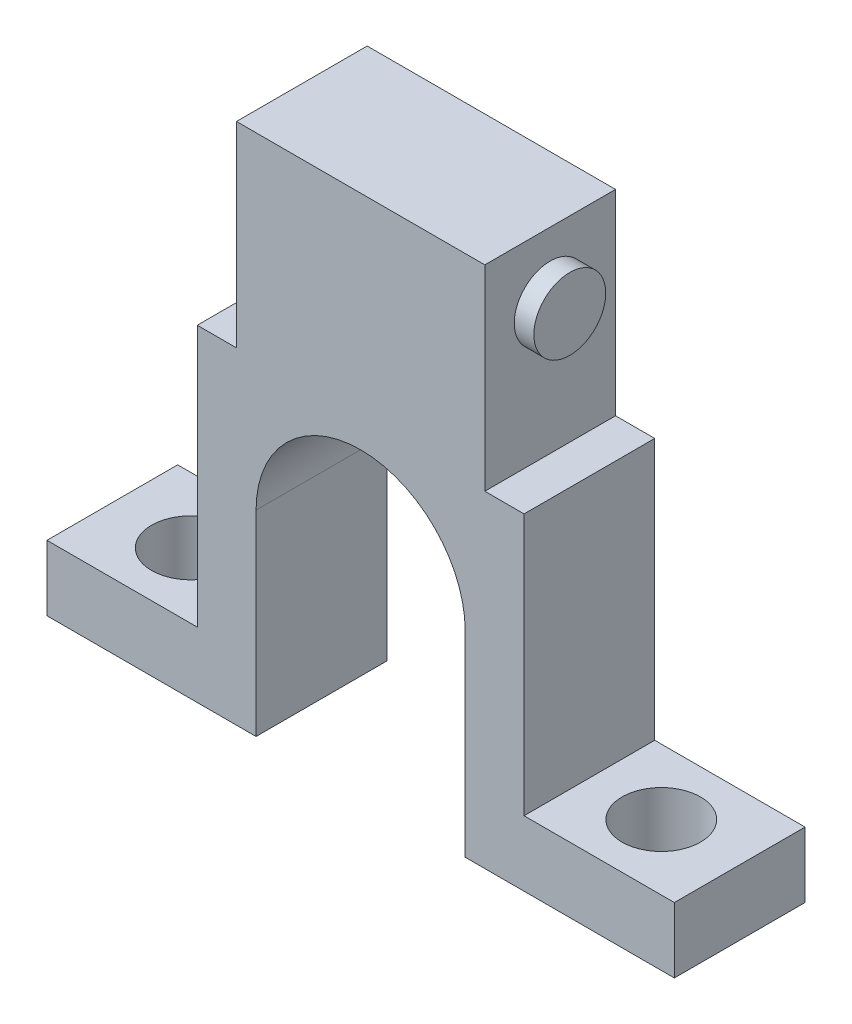
SolidWorks part; units mm, degrees
ref_plane "Front Plane" through (0, 0, 0) normal (0, 0, 1) x (1, 0, 0)
ref_plane "Top Plane" through (0, 0, 0) normal (0, 1, 0) x (1, 0, 0)
ref_plane "Right Plane" through (0, 0, 0) normal (1, 0, 0) x (0, 0, -1)
sketch "Sketch1" plane through (0, 0, 0) normal (0, 0, 1) x (1, 0, 0)
  line L0 (0, 0) -> (0, 17.5) construction
  line L1 (-9.5, 17.5) -> (9.5, 17.5)
  line L2 (9.5, 2.5) -> (12.5, 2.5)
  line L3 (-12.5, -17.5) -> (12.5, -17.5)
  line L4 (12.5, 2.5) -> (12.5, -17.5)
  line L5 (0, 0) -> (0, -17.5) construction
  line L6 (9.5, 17.5) -> (9.5, 2.5)
  line L7 (-9.5, 2.5) -> (-12.5, 2.5)
  line L8 (-9.5, 17.5) -> (-9.5, 2.5)
  line L9 (-12.5, 2.5) -> (-12.5, -17.5)
  dimension "D1" = 19
  dimension "D2" = 35
  dimension "D3" = 25
  dimension "D4" = 15
extrude "Boss-Extrude1" add sketch "Sketch1" along normal mid plane 10
sketch "Sketch4" plane through (0, 0, 0) normal (1, 0, 0) x (0, 0, -1)
  line L0 (0, 12.5) -> (0, 0) construction
  line L2 (-5, 17.5) -> (5, 17.5) construction
  circle A0 centre (0, 12.5) radius 2.75
  dimension "D1" = 5.5
  dimension "D2" = 5
extrude "Boss-Extrude3" add sketch "Sketch4" along normal mid plane 22
sketch "Sketch6" plane through (0, -17.5, 0) normal (0, -1, 0) x (1, 0, 0)
  line L1 (-24, 5) -> (24, 5)
  line L2 (-24, 5) -> (-24, -5)
  line L3 (-24, -5) -> (24, -5)
  line L4 (24, 5) -> (24, -5)
  line L5 (-12.5, -5) -> (12.5, -5) construction
  line L6 (0, 5) -> (0, 0) construction
  line L8 (-12.5, 5) -> (12.5, 5) construction
  dimension "D1" = 48
extrude "Boss-Extrude4" add sketch "Sketch6" along normal blind 5
sketch "Sketch7" plane through (0, -17.5, 0) normal (0, 1, 0) x (1, 0, 0)
  line L0 (-18, 0) -> (18, 0) construction
  circle A0 centre (-18, 0) radius 3
  circle A1 centre (18, 0) radius 3
  point P5 (0, 0)
  dimension "D2" = 6
  dimension "D1" = 36
extrude "Cut-Extrude2" cut sketch "Sketch7" against normal through all
sketch "Sketch8" plane through (0, 0, 5) normal (0, 0, 1) x (1, 0, 0)
  line L0 (0, -22.5) -> (0, -7.5) construction
  line L1 (24, -22.5) -> (-24, -22.5) construction
  line L2 (-8, -22.5) -> (-8, -7.5)
  line L3 (8, -22.5) -> (8, -7.5)
  arc A0 (-8, -22.5) -> (8, -22.5) centre (0, -22.5) ccw
  arc A1 (8, -7.5) -> (-8, -7.5) centre (0, -7.5) ccw
  point P5 (0, -15)
  dimension "D2" = 8
  dimension "D1" = 15
extrude "Cut-Extrude3" cut sketch "Sketch8" against normal through all
